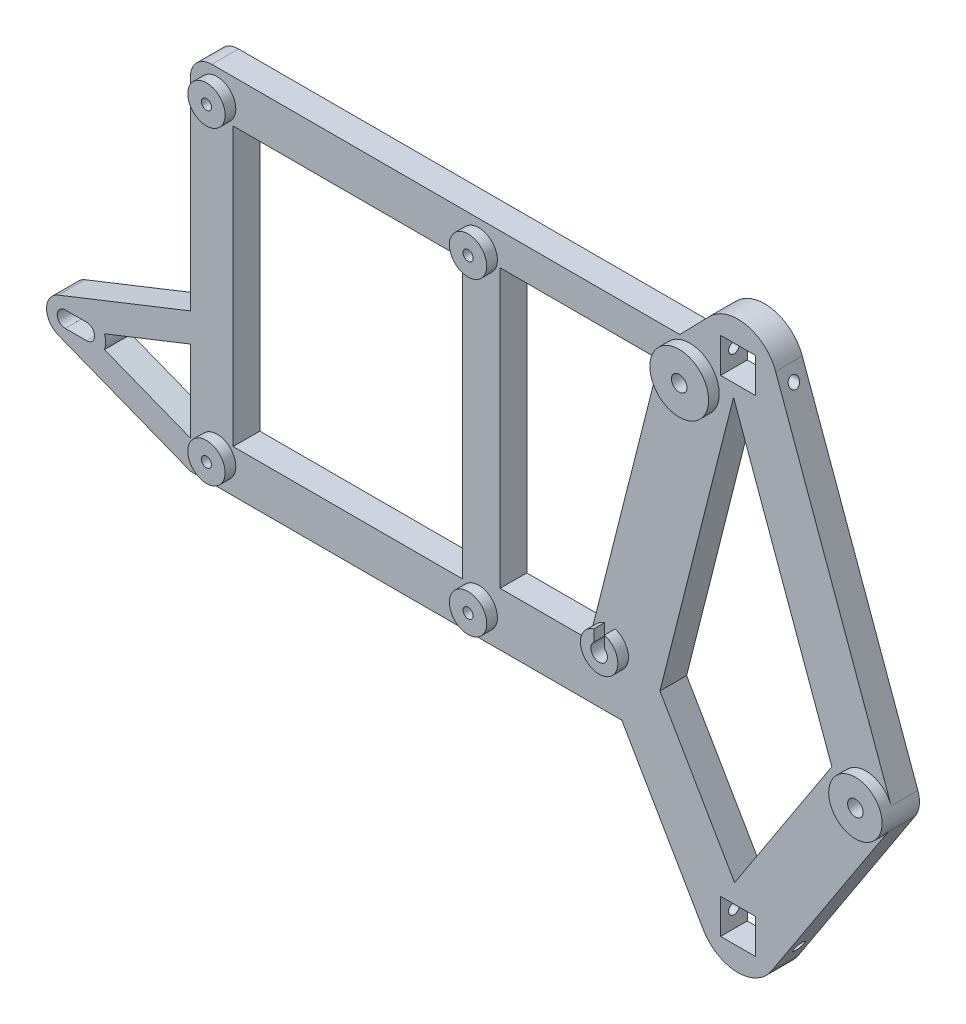
SolidWorks part; units mm, degrees
ref_plane "Front Plane" through (0, 0, 0) normal (0, 0, 1) x (1, 0, 0)
ref_plane "Top Plane" through (0, 0, 0) normal (0, 1, 0) x (1, 0, 0)
ref_plane "Right Plane" through (0, 0, 0) normal (1, 0, 0) x (0, 0, -1)
sketch "Sketch1" plane through (0, 0, 0) normal (0, 0, 1) x (1, 0, 0)
  line L0 (22, 81) -> (24, 83)
  line L1 (0, 0) -> (70, 0)
  line L2 (0, 0) -> (0, 81)
  line L3 (0, 81) -> (22, 81)
  line L4 (70, 0) -> (70, 81)
  line L5 (57, 83) -> (59, 81)
  line L6 (22.0536, 84.4309) -> (29.6185, 92.224)
  line L7 (24, 83) -> (57, 83)
  line L8 (20.657, 81.9045) -> (7.6067, 30.2574)
  line L9 (-92.2897, 34.7537) -> (-67.55, 44.56)
  line L10 (59, 81) -> (70, 81)
  line L11 (-66, -2) -> (-10, -2)
  line L12 (-66, -2) -> (-66, 85)
  line L13 (-66, 85) -> (-10, 85)
  line L14 (7.9725, 27.6437) -> (28.5126, -7.7634)
  line L15 (41.2808, -8.099) -> (63.1872, 25.4673)
  line L16 (42.05, 89.5587) -> (63.7, 29.9058)
  line L17 (-10, -2) -> (-10, 85)
  line L19 (-91, 33) -> (-87, 33)
  line L20 (-91, 33) -> (-91, 29.9972)
  line L21 (-91, 29.9972) -> (-87, 29.9972)
  line L22 (-87, 33) -> (-87, 29.9972)
  line L26 (-9.55, 86.56) -> (-63.55, 86.56)
  line L27 (-9.55, 86.56) -> (-9.55, 18.56)
  line L28 (-9.55, 18.56) -> (-67.55, 18.56)
  line L29 (-67.55, 82.56) -> (-67.55, 18.56)
  line L30 (-59.55, 78.56) -> (-16.55, 78.56)
  line L31 (-59.55, 78.56) -> (-59.55, 26.56)
  line L32 (-59.55, 26.56) -> (-16.55, 26.56)
  line L33 (-16.55, 78.56) -> (-16.55, 26.56)
  line L34 (-9.55, 18.56) -> (17.5615, 18.56)
  line L35 (-9.55, 18.56) -> (-9.55, 28.56)
  line L36 (-9.55, 28.56) -> (17.5615, 28.56)
  line L37 (17.5615, 18.56) -> (17.5615, 28.56)
  line L38 (-9.55, 86.56) -> (28.051, 86.56)
  line L39 (-9.55, 86.56) -> (-9.55, 80.56)
  line L40 (-9.55, 80.56) -> (28.051, 80.56)
  line L41 (28.051, 86.56) -> (28.051, 80.56)
  line L42 (-92.276, 28.2409) -> (-67.55, 18.56)
  line L43 (-86.9076, 31.5086) -> (-67.55, 23.9296)
  line L44 (-86.9076, 31.5086) -> (-67.55, 39.1815)
  line L46 (31.75, -0.75) -> (38.25, -0.75)
  line L47 (31.75, -0.75) -> (31.75, -7.25)
  line L48 (31.75, -7.25) -> (38.25, -7.25)
  line L49 (38.25, -0.75) -> (38.25, -7.25)
  line L50 (31.75, 90.25) -> (38.25, 90.25)
  line L51 (31.75, 90.25) -> (31.75, 83.75)
  line L52 (31.75, 83.75) -> (38.25, 83.75)
  line L53 (38.25, 90.25) -> (38.25, 83.75)
  circle A0 centre (11, 29.4) radius 1.55
  circle A1 centre (59, 28.2) radius 1.45
  circle A2 centre (26, 80.6) radius 1.45
  circle A3 centre (35, 87) radius 3.25
  circle A4 centre (35, -4) radius 3.25
  circle A5 centre (26, 80.6) radius 5.5
  circle A6 centre (35, 87) radius 7.5
  circle A7 centre (59, 28.2) radius 5
  circle A8 centre (35, -4) radius 7.5
  circle A9 centre (11, 29.4) radius 3.5
  circle A10 centre (-62.55, 81.56) radius 0.95
  circle A11 centre (-13.55, 81.56) radius 0.95
  circle A12 centre (-62.55, 23.56) radius 0.95
  circle A13 centre (-13.55, 23.56) radius 0.95
  circle A14 centre (-62.55, 81.56) radius 3.5
  circle A15 centre (-13.55, 81.56) radius 3.5
  circle A16 centre (-13.55, 23.56) radius 3.5
  circle A17 centre (-62.55, 23.56) radius 3.5
  circle A18 centre (-91, 31.5) radius 1.5
  circle A19 centre (-91, 31.5) radius 3.5
  arc A20 (-63.55, 86.56) -> (-67.55, 82.56) centre (-63.55, 82.56) ccw
  circle A21 centre (-87, 31.4972) radius 1.5
  circle A22 centre (-86.9076, 31.5086) radius 3.5
  dimension "D5" = 3.1
  dimension "D7" = 2.9
  dimension "D8" = 2.9
  dimension "D14" = 6.5
  dimension "D15" = 6.5
  dimension "D20" = 15
  dimension "D21" = 11
  dimension "D22" = 10
  dimension "D23" = 15
  dimension "D24" = 7
  dimension "D25" = 1.9
  dimension "D26" = 1.9
  dimension "D27" = 1.9
  dimension "D28" = 1.9
  dimension "D41" = 7
  dimension "D42" = 7
  dimension "D43" = 7
  dimension "D44" = 7
  dimension "D54" = 3
  dimension "D56" = 7
  dimension "D62" = 4
  dimension "D53" = 126
  dimension "D63" = 3
  dimension "D65" = 7
  dimension "D1" = 81
  dimension "D2" = 70
  dimension "D3" = 33
  dimension "D4" = 29.4
  dimension "D6" = 2
  dimension "D9" = 11
  dimension "D10" = 28.2
  dimension "D11" = 11
  dimension "D12" = 26
  dimension "D13" = 2.4
  dimension "D16" = 0
  dimension "D17" = 35
  dimension "D18" = 91
  dimension "D19" = 4
  dimension "D29" = 49
  dimension "D30" = 49
  dimension "D31" = 58
  dimension "D32" = 58
  dimension "D33" = 56
  dimension "D34" = 87
  dimension "D35" = 25.56
  dimension "D36" = 3.45
  dimension "D37" = 10
  dimension "D38" = 2
  dimension "D39" = 3.45
  dimension "D40" = 25.56
  dimension "D45" = 5
  dimension "D46" = 5
  dimension "D47" = 5
  dimension "D48" = 3
  dimension "D49" = 3
  dimension "D50" = 3
  dimension "D51" = 3
  dimension "D52" = 4
  dimension "D55" = 35.5
  dimension "D57" = 26
  dimension "D58" = 5
  dimension "D59" = 5
  dimension "D60" = 10
  dimension "D61" = 6
  dimension "D64" = 4
  dimension "D66" = 1.5028
  dimension "D67" = 4
extrude "Boss-Extrude1" add sketch "Sketch1" along normal blind 5
sketch "Sketch3" plane through (0, 0, 5) normal (0, 0, 1) x (1, 0, 0)
  line L0 (10, 30.5843) -> (10, 32.7541)
  line L4 (12, 30.5843) -> (12, 32.7541)
  circle A0 centre (26, 80.6) radius 1.45
  circle A1 centre (59, 28.2) radius 1.45
  circle A2 centre (59, 28.2) radius 5
  circle A3 centre (26, 80.6) radius 5.5
  arc A4 (10, 30.5843) -> (12, 30.5843) centre (11, 29.4) ccw
  arc A5 (10, 32.7541) -> (12, 32.7541) centre (11, 29.4) ccw
  circle A6 centre (-13.55, 23.56) radius 3.5
  circle A7 centre (-13.55, 81.56) radius 3.5
  circle A8 centre (-62.55, 81.56) radius 3.5
  circle A9 centre (-62.55, 23.56) radius 3.5
  circle M20 centre (26, 80.6) radius 1.45
  circle M21 centre (59, 28.2) radius 1.45
  arc M35 (7.6067, 30.2574) -> (7.6023, 28.56) centre (11, 29.4) ccw
  circle M37 centre (11, 29.4) radius 1.55
  circle M53 centre (-62.55, 23.56) radius 0.95
  circle M54 centre (-13.55, 81.56) radius 0.95
  circle M55 centre (-62.55, 81.56) radius 0.95
  circle M56 centre (-13.55, 23.56) radius 0.95
  dimension "D1" = 11
  dimension "D2" = 10
  dimension "D3" = 7
  dimension "D4" = 2
  dimension "D5" = 7
  dimension "D6" = 7
  dimension "D7" = 7
  dimension "D8" = 7
extrude "Boss-Extrude3" add sketch "Sketch3" along normal blind 2 contours A2 M21 | A3 M20 | L0 A5 L4 M35 M37 | A6 M56 | A9 M53 | A8 M55 | A7 M54
sketch "Sketch4" plane through (0, 0, 5) normal (0, 0, 1) x (1, 0, 0)
  line L0 (34.1744, 81.4227) -> (52.5884, 30.6862)
  line L1 (52.5884, 30.6862) -> (34.3753, 2.7791)
  line L2 (34.3753, 2.7791) -> (20.393, 26.882)
  line L3 (20.393, 26.882) -> (34.1744, 81.4227)
  line L4 (42.05, 89.5587) -> (63.7, 29.9058) construction
  line L5 (41.2808, -8.099) -> (63.1872, 25.4673) construction
  line L8 (13.2421, 18.56) -> (28.5126, -7.7634) construction
  line L9 (20.3172, 80.56) -> (7.6067, 30.2574) construction
extrude "Cut-Extrude1" cut sketch "Sketch4" against normal blind 10
sketch "Sketch6" plane through (38.25, 0, 0) normal (-1, 0, 0) x (0, 0, 1)
  line L0 (0, 90.25) -> (0, 83.75) construction
  line L1 (5, 90.25) -> (0, 90.25) construction
  line L2 (0, -0.75) -> (0, -7.25) construction
  line L3 (5, -0.75) -> (0, -0.75) construction
  circle A0 centre (2.5, -4) radius 1
  circle A1 centre (2.5, 87) radius 1
  dimension "D1" = 2
  dimension "D4" = 2
  dimension "D2" = 2.5
  dimension "D3" = 3.25
  dimension "D5" = 2.5
  dimension "D6" = 3.25
extrude "Cut-Extrude2" cut sketch "Sketch6" against normal blind 10 and the other way blind 14.13
